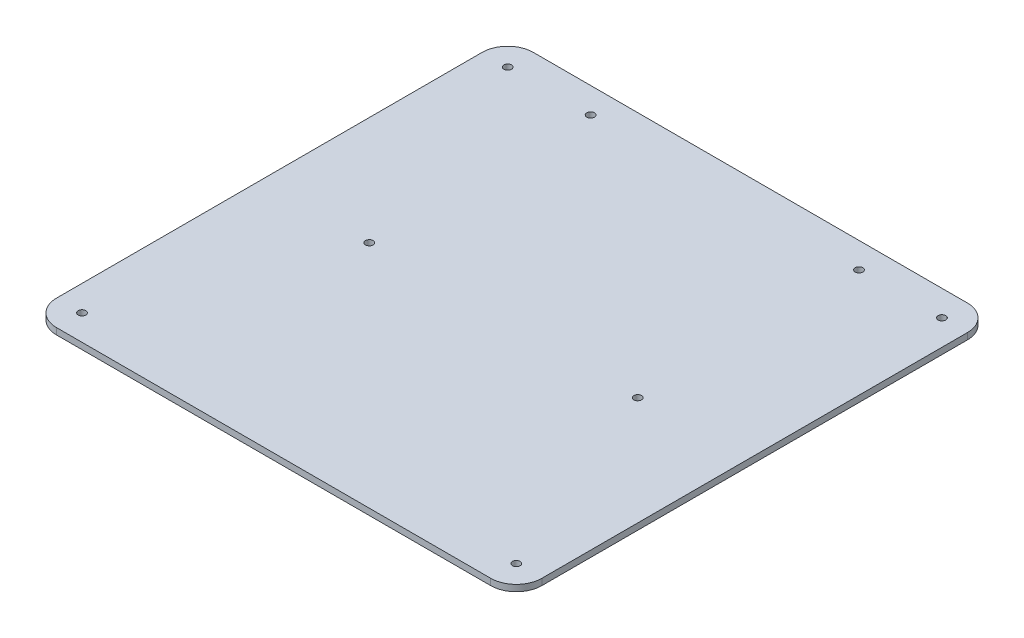
SolidWorks part; units mm, degrees
ref_plane "前视基准面" through (0, 0, 0) normal (0, 0, 1) x (1, 0, 0)
ref_plane "上视基准面" through (0, 0, 0) normal (0, 1, 0) x (1, 0, 0)
ref_plane "右视基准面" through (0, 0, 0) normal (1, 0, 0) x (0, 0, -1)
sketch "草图1" plane through (0, 67.1371, 0) normal (0, 1, 0) x (1, 0, 0)
  line L0 (16.9005, -171.7273) -> (16.9005, 28.2727) construction
  line L1 (1.9005, 39.9177) -> (-168.0995, 39.9177)
  line L2 (11.9005, 29.9177) -> (11.9005, -136.7273)
  line L3 (1.9005, -146.7273) -> (-168.0995, -146.7273)
  line L4 (-178.0995, 29.9177) -> (-178.0995, -136.7273)
  line L5 (-183.0995, 28.2727) -> (-183.0995, -171.7273) construction
  line L6 (-133.0995, -141.7273) -> (-33.0995, -141.7273) construction
  line L7 (-30.5685, 34.9177) -> (-135.6304, 34.9177) construction
  arc A0 (-178.0995, 29.9177) -> (-168.0995, 39.9177) centre (-168.0995, 29.9177) cw
  arc A1 (-178.0995, -136.7273) -> (-168.0995, -146.7273) centre (-168.0995, -136.7273) ccw
  arc A2 (1.9005, -146.7273) -> (11.9005, -136.7273) centre (1.9005, -136.7273) ccw
  arc A3 (1.9005, 39.9177) -> (11.9005, 29.9177) centre (1.9005, 29.9177) cw
  circle A4 centre (-30.5685, 29.9177) radius 1.5
  circle A5 centre (-135.6304, 29.9177) radius 1.5
  circle A6 centre (-135.6304, -56.7273) radius 1.5
  circle A7 centre (-30.5685, -56.7273) radius 1.5
  circle A8 centre (1.9005, 29.9177) radius 1.5
  circle A9 centre (1.9005, -136.7273) radius 1.5
  circle A10 centre (-168.0995, -136.7273) radius 1.5
  circle A11 centre (-168.0995, 29.9177) radius 1.5
  dimension "D4" = 10
  dimension "D6" = 3
  dimension "D7" = 3
  dimension "D8" = 3
  dimension "D9" = 3
  dimension "D1" = 5
  dimension "D2" = 5
  dimension "D3" = 5
  dimension "D5" = 5
extrude "凸台-拉伸1" add sketch "草图1" along normal blind 2.5
